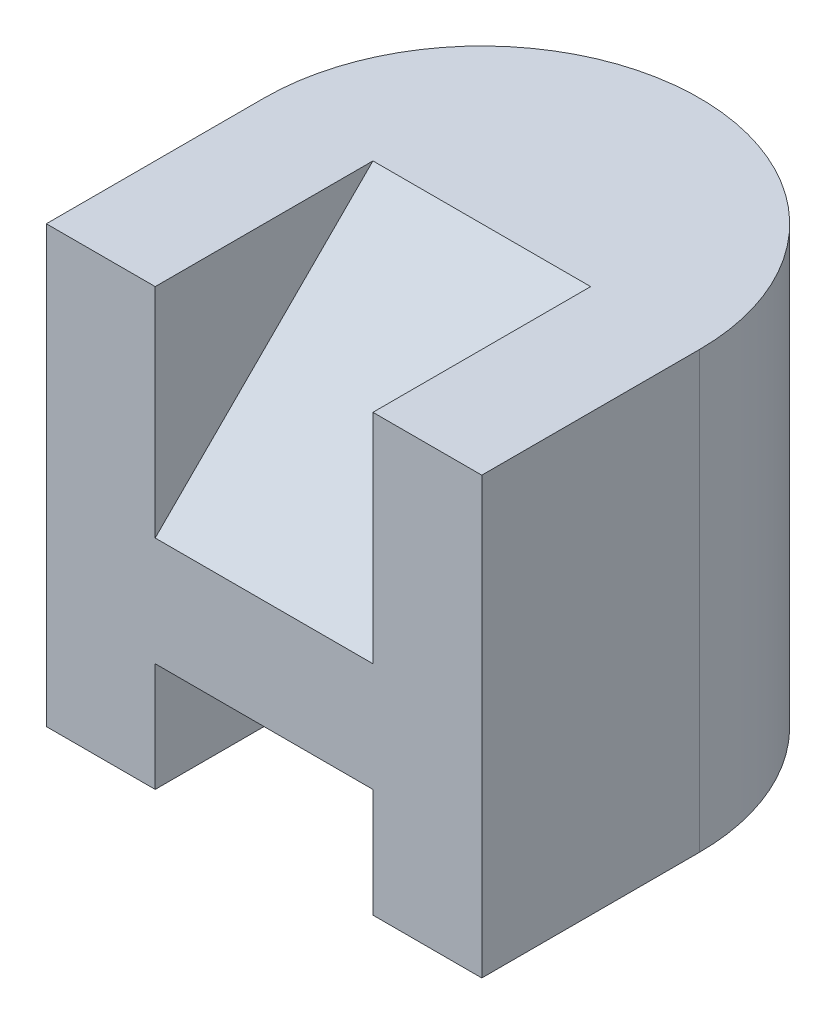
SolidWorks part; units mm, degrees
ref_plane "Front" through (0, 0, 0) normal (0, 0, 1) x (1, 0, 0)
ref_plane "Top" through (0, 0, 0) normal (0, 1, 0) x (1, 0, 0)
ref_plane "Right" through (0, 0, 0) normal (1, 0, 0) x (0, 0, -1)
sketch "Sketch1" plane through (0, 0, 0) normal (0, 1, 0) x (1, 0, 0)
  line L0 (-2, -2) -> (-2, 0)
  line L1 (2, 0) -> (2, -2)
  line L2 (2, -2) -> (-2, -2)
  arc A0 (-2, 0) -> (2, 0) centre (0, 0) cw
  dimension "D3" = 0
  dimension "D1" = 4
  dimension "D2" = 2
extrude "Boss-Extrude1" add sketch "Sketch1" along normal blind 4
sketch "Sketch2" plane through (0, 0, 2) normal (0, 0, 1) x (1, 0, 0)
  line L0 (-2, 0) -> (2, 0) construction
  line L1 (-1, 0) -> (1, 0)
  line L2 (-1, 0) -> (-1, 1)
  line L3 (-1, 1) -> (1, 1)
  line L4 (1, 0) -> (1, 1)
  dimension "D1" = 2
  dimension "D2" = 1
  dimension "D3" = 1
extrude "Cut-Extrude1" cut sketch "Sketch2" against normal blind 4
sketch "Sketch3" plane through (0, 0, 0) normal (1, 0, 0) x (0, 0, -1)
  line L0 (0, 4) -> (-2, 2)
  line L1 (-2, 4) -> (-2, 0) construction
  line L2 (-2, 2) -> (-2, 4)
  line L3 (-2, 4) -> (0, 4)
extrude "Cut-Extrude2" cut sketch "Sketch3" against normal mid plane 2
